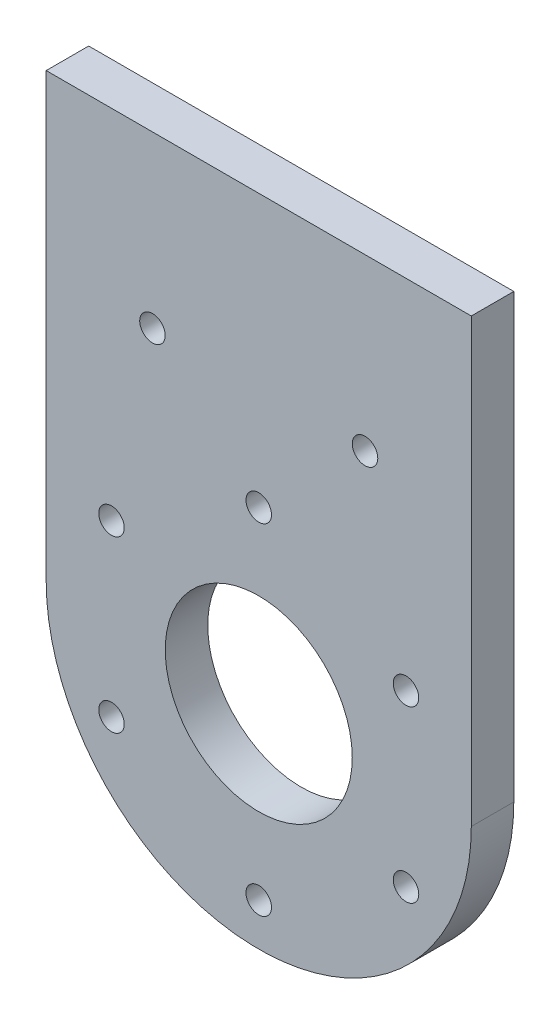
SolidWorks part; units mm, degrees
ref_plane "Plan de face" through (0, 0, 0) normal (0, 0, 1) x (1, 0, 0)
ref_plane "Plan de dessus" through (0, 0, 0) normal (0, 1, 0) x (1, 0, 0)
ref_plane "Plan de droite" through (0, 0, 0) normal (1, 0, 0) x (0, 0, -1)
sketch "Esquisse1" plane through (0, 0, 0) normal (0, 0, 1) x (1, 0, 0)
  line L0 (-50, 52) -> (50, 52)
  line L1 (-50, 52) -> (-50, -48.5481)
  line L2 (50, 52) -> (50, -48.5481)
  line L3 (-50, -48.5481) -> (50, -48.5481)
  circle A1 centre (0, 0) radius 11
  dimension "D1" = 52
extrude "Boss.-Extru.1" add sketch "Esquisse1" along normal blind 5
sketch "Esquisse2" plane through (0, 0, 5) normal (0, 0, 1) x (1, 0, 0)
  line L0 (-25, 0) -> (25, 0)
  line L1 (-25, 0) -> (-25, 55)
  line L2 (25, 0) -> (25, 55)
  line L3 (-25, 55) -> (25, 55)
  line L4 (-50, 52) -> (50, 52) construction
  circle A0 centre (0, 20) radius 1.5
  circle A1 centre (17.3205, 10) radius 1.5
  circle A2 centre (17.3205, -10) radius 1.5
  circle A3 centre (0, -20) radius 1.5
  circle A4 centre (-17.3205, -10) radius 1.5
  circle A5 centre (-17.3205, 10) radius 1.5
  circle A6 centre (0, 0) radius 25
  circle A13 centre (-12.5, 32) radius 1.5
  circle A14 centre (12.5, 32) radius 1.5
  point P4 (0, 0)
  point P12 (0, 0)
  point P32 (0, 0)
  point P33 (0, 0)
  dimension "D1" = 20
  dimension "D3" = 55
  dimension "D8" = 12.5
  dimension "D9" = 12.5
  dimension "D10" = 20
  dimension "D11" = 20
  dimension "D2" = 6
extrude "Enlèv. mat.-Extru.1" cut sketch "Esquisse2" against normal through all
